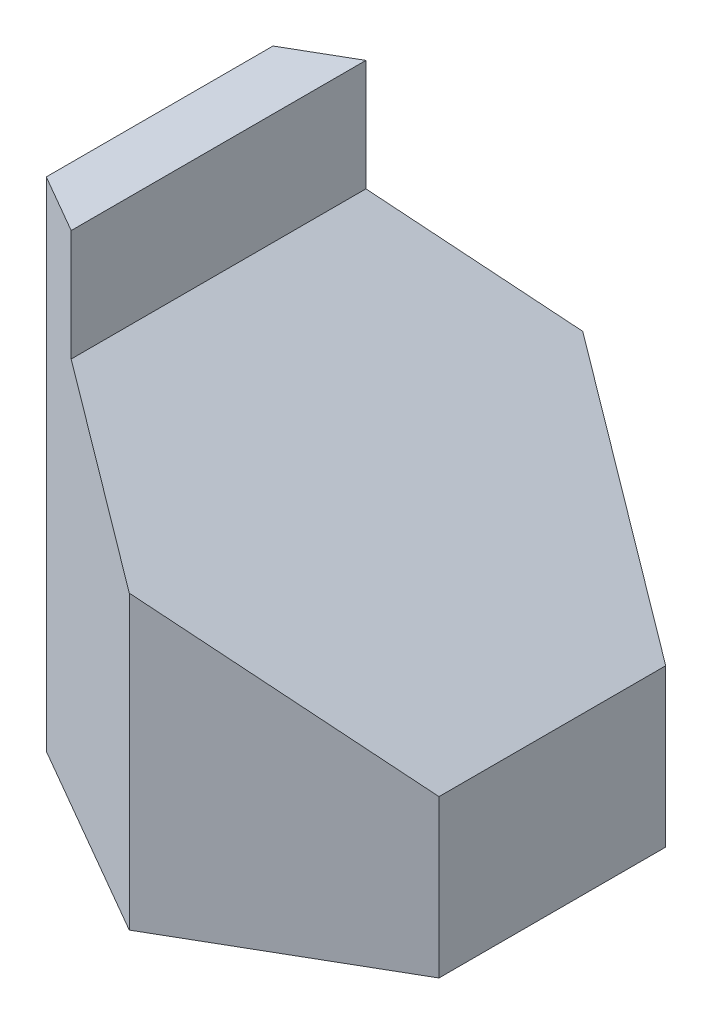
SolidWorks part; units mm, degrees
ref_plane "前视基准面" through (0, 0, 0) normal (0, 0, 1) x (1, 0, 0)
ref_plane "上视基准面" through (0, 0, 0) normal (0, 1, 0) x (1, 0, 0)
ref_plane "右视基准面" through (0, 0, 0) normal (1, 0, 0) x (0, 0, -1)
sketch "草图1" plane through (0, 0, 0) normal (0, 1, 0) x (1, 0, 0)
  line L1 (0, 34.641) -> (-30, 17.3205)
  line L2 (-30, 17.3205) -> (-30, -17.3205)
  line L3 (-30, -17.3205) -> (0, -34.641)
  line L4 (0, -34.641) -> (30, -17.3205)
  line L5 (30, -17.3205) -> (30, 17.3205)
  line L6 (30, 17.3205) -> (0, 34.641)
extrude "凸台-拉伸2" add sketch "草图1" along normal blind 76
ref_plane "基准面3" through (30, 0, 0) normal (1, 0, 0) x (0, 0, -1)
sketch "草图5" plane through (30, 0, 0) normal (1, 0, 0) x (0, 0, -1)
  line L0 (34.641, 76) -> (34.641, 0) construction
  line L1 (-34.641, 76) -> (34.641, 76)
  line L2 (-34.641, 76) -> (-34.641, 59)
  line L3 (-34.641, 59) -> (34.641, 59)
  line L4 (34.641, 76) -> (34.641, 59)
extrude "切除-拉伸2" cut sketch "草图5" against normal blind 51
sketch "草图6" plane through (30, 0, 0) normal (1, 0, 0) x (0, 0, -1)
  line L0 (-17.3205, 0) -> (17.3205, 0)
  line L1 (-17.3205, 24) -> (17.3205, 24)
ref_plane "基准面4" through (20.8024, 30.3121, 0) normal (-0.5658, -0.8245, 0) x (-0.8245, 0.5658, 0)
sketch "草图7" plane through (20.8024, 30.3121, 0) normal (-0.5658, -0.8245, 0) x (-0.8245, 0.5658, 0)
  line L1 (50.6995, 36.6018) -> (-29.1171, 36.6018)
  line L2 (50.6995, 36.6018) -> (50.6995, -36.8092)
  line L3 (50.6995, -36.8092) -> (-29.1171, -36.8092)
  line L4 (-29.1171, 36.6018) -> (-29.1171, -36.8092)
extrude "切除-拉伸3" cut sketch "草图7" against normal blind 51
